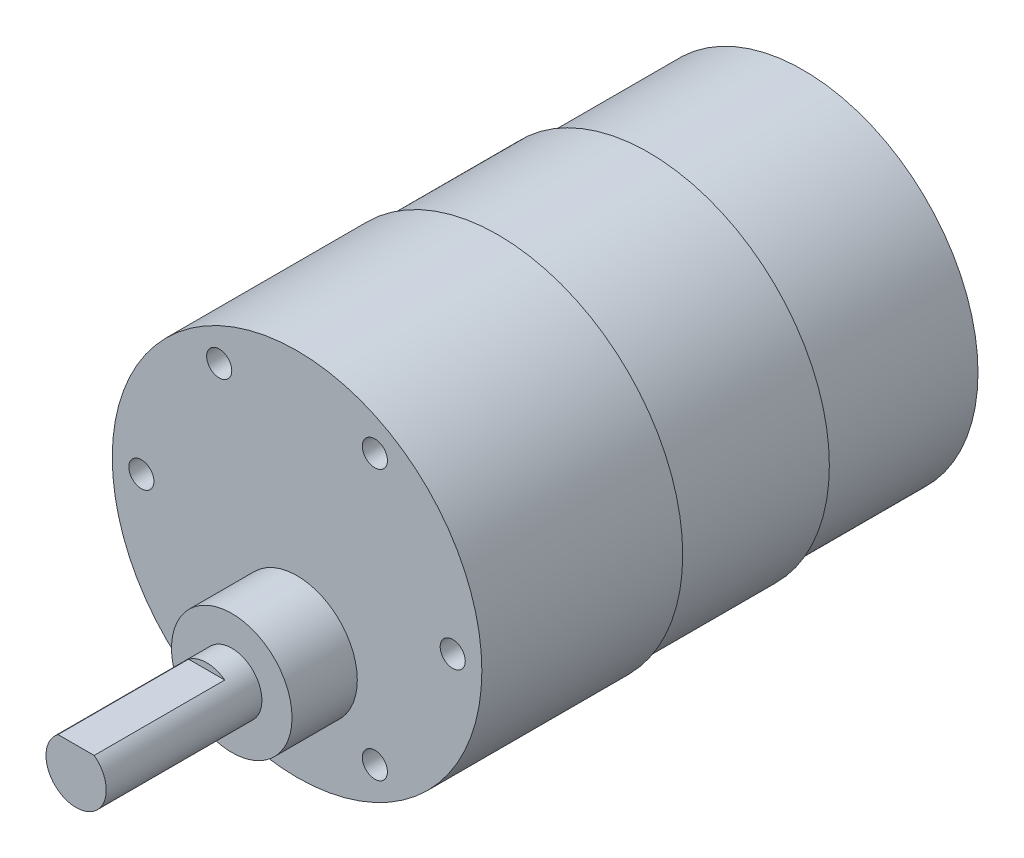
SolidWorks part; units mm, degrees
ref_plane "Front Plane" through (0, 0, 0) normal (0, 0, 1) x (1, 0, 0)
ref_plane "Top Plane" through (0, 0, 0) normal (0, 1, 0) x (1, 0, 0)
ref_plane "Right Plane" through (0, 0, 0) normal (1, 0, 0) x (0, 0, -1)
sketch "Sketch1" plane through (0, 0, 0) normal (0, 0, 1) x (1, 0, 0)
  circle A0 centre (0, 0) radius 17.4
  dimension "D1" = 34.8
extrude "Boss-Extrude1" add sketch "Sketch1" along normal blind 15.4
sketch "Sketch2" plane through (0, 0, 15.4) normal (0, 0, 1) x (1, 0, 0)
  circle A0 centre (0, 0) radius 18
  dimension "D1" = 36
extrude "Boss-Extrude2" add sketch "Sketch2" along normal blind 15
sketch "Sketch3" plane through (0, 0, 30.4) normal (0, 0, 1) x (1, 0, 0)
  circle A0 centre (0, 0) radius 18.4
  dimension "D1" = 36.8
extrude "Boss-Extrude3" add sketch "Sketch3" along normal blind 20
sketch "Sketch4" plane through (0, 0, 50.4) normal (0, 0, 1) x (1, 0, 0)
  circle A0 centre (0, -7) radius 6
  dimension "D2" = 12
  dimension "D1" = 7
extrude "Boss-Extrude4" add sketch "Sketch4" along normal blind 6.5
sketch "Sketch5" plane through (0, 0, 56.9) normal (0, 0, 1) x (1, 0, 0)
  circle A0 centre (0, -7) radius 3
  dimension "D1" = 6
extrude "Boss-Extrude5" add sketch "Sketch5" along normal blind 15.5
sketch "Sketch6" plane through (0, 0, 72.4) normal (0, 0, 1) x (1, 0, 0)
  line L0 (-1.8, -4.6) -> (1.8, -4.6)
  circle A0 centre (0, -7) radius 3 construction
  circle A1 centre (0, -7) radius 3 construction
  arc A2 (-1.8, -4.6) -> (1.8, -4.6) centre (0, -7) cw
  dimension "D1" = 2.4
extrude "Cut-Extrude1" cut sketch "Sketch6" against normal blind 13
hole_wizard "Tap Drill for M3x0.5 Tap1" positions "Sketch7" profile "Sketch8" hole size "M3x0.5" standard "ANSI Metric"
sketch "Sketch7" plane through (0, 0, 50.4) normal (0, 0, 1) x (1, 0, 0)
  circle A0 centre (0, 0) radius 15.5
  point P0 (-15.5, 0)
  point P13 (-7.75, 13.4234)
  point P14 (7.75, 13.4234)
  point P15 (15.5, 0)
  point P16 (7.75, -13.4234)
  point P17 (-7.75, -13.4234)
  dimension "D1" = 15.5
  dimension "D2" = 6
sketch "Sketch8" plane through (-15.5, 0, 50.4) normal (1, 0, 0) x (0, -1, 0)
  line L0 (0, 0) -> (0, 10.76)
  line L1 (0, 10.76) -> (1.25, 10.76)
  line L2 (1.25, 10.76) -> (1.25, 0)
  line L5 (1.25, 0) -> (0, 0)
  line L10 (0, 10.76) -> (-1.25, 10.76) construction
  line L11 (0, -6.35) -> (0, 107.95) construction
  dimension "Hole Dia." = 2.5
  dimension "Hole Depth" = 10.76
  dimension "Drill Angle" = 180
